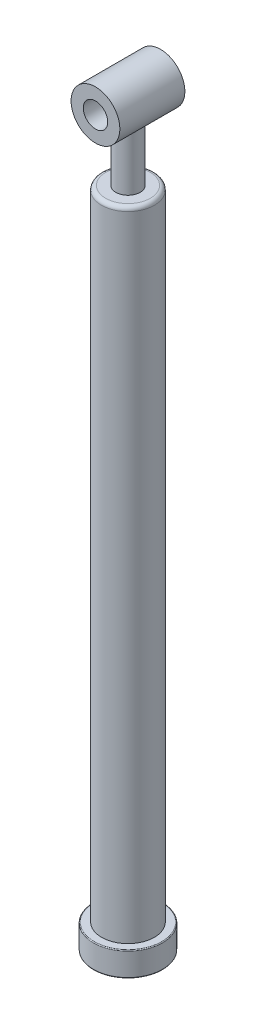
SolidWorks part; units mm, degrees
ref_plane "Front Plane" through (0, 0, 0) normal (0, 0, 1) x (1, 0, 0)
ref_plane "Top Plane" through (0, 0, 0) normal (0, 1, 0) x (1, 0, 0)
ref_plane "Right Plane" through (0, 0, 0) normal (1, 0, 0) x (0, 0, -1)
sketch "Sketch1" plane through (0, 0, 0) normal (0, 1, 0) x (1, 0, 0)
  circle A0 centre (0, 0) radius 32.5
  dimension "D1" = 65
extrude "Boss-Extrude1" add sketch "Sketch1" along normal mid plane 785
fillet "Fillet1" radius 5 1 edges at (0, 392.5, 32.5)
sketch "Sketch2" plane through (0, -392.5, 0) normal (0, -1, 0) x (1, 0, 0)
  circle A0 centre (0, 0) radius 42.5
  dimension "D1" = 85
extrude "Boss-Extrude2" add sketch "Sketch2" along normal blind 30
sketch "Sketch3" plane through (0, -422.5, 0) normal (0, -1, 0) x (1, 0, 0)
  circle A0 centre (0, 0) radius 20
  dimension "D1" = 40
extrude "Cut-Extrude1" cut sketch "Sketch3" against normal blind 810
sketch "Sketch4" plane through (0, 0, 0) normal (0, 0, 1) x (1, 0, 0)
  line L0 (27.5, 392.5) -> (-27.5, 392.5) construction
  circle A0 centre (0, 487.5) radius 30
  circle A1 centre (0, 487.5) radius 15
  point P3 (0, 0)
  dimension "D1" = 95
  dimension "D2" = 60
  dimension "D3" = 30
extrude "Boss-Extrude3" add sketch "Sketch4" along normal mid plane 80 separate body
sketch "Sketch5" plane through (0, 392.5, 0) normal (0, 1, 0) x (1, 0, 0)
  circle A0 centre (0, 0) radius 15
  dimension "D1" = 30
extrude "Boss-Extrude4" add sketch "Sketch5" along normal up to next
fillet "Fillet2" radius 1 2 edges at (0, -422.5, -42.5) (0, -392.5, -42.5)
